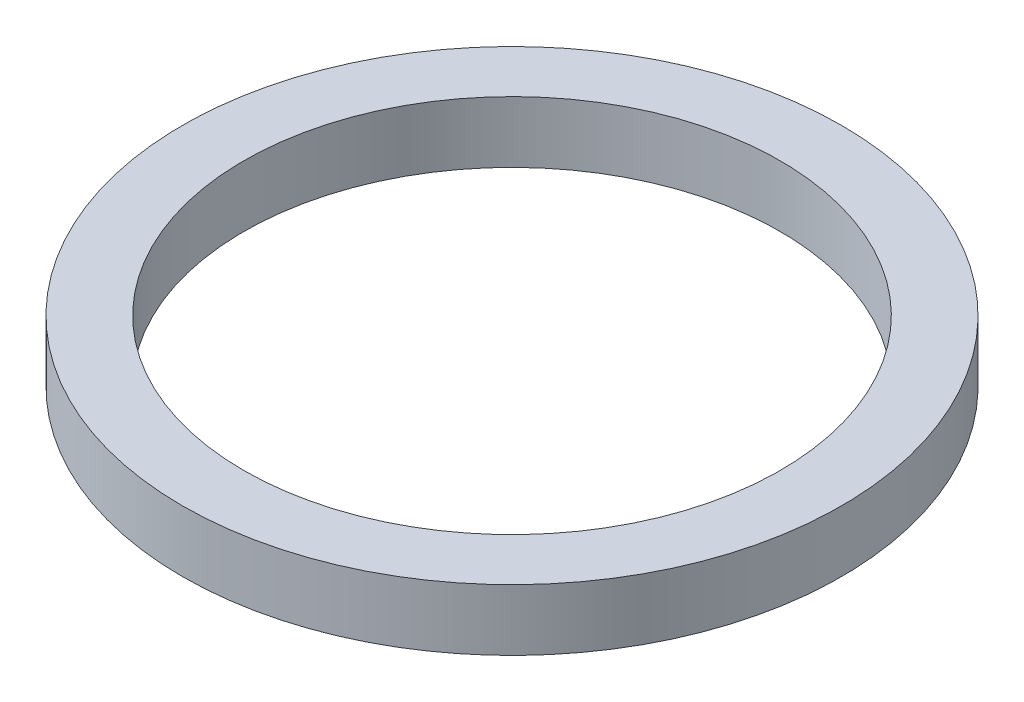
SolidWorks part; units mm, degrees
material "不锈钢 (铁素体)"
ref_plane "前视基准面" through (0, 0, 0) normal (0, 0, 1) x (1, 0, 0)
ref_plane "上视基准面" through (0, 0, 0) normal (0, 1, 0) x (1, 0, 0)
ref_plane "右视基准面" through (0, 0, 0) normal (1, 0, 0) x (0, 0, -1)
sketch "草图1" plane through (0, 0, 0) normal (0, 1, 0) x (1, 0, 0)
  circle A0 centre (0, 0) radius 35
  circle A1 centre (0, 0) radius 43
  dimension "D1" = 70
  dimension "D2" = 86
extrude "凸台-拉伸1" add sketch "草图1" along normal blind 8
